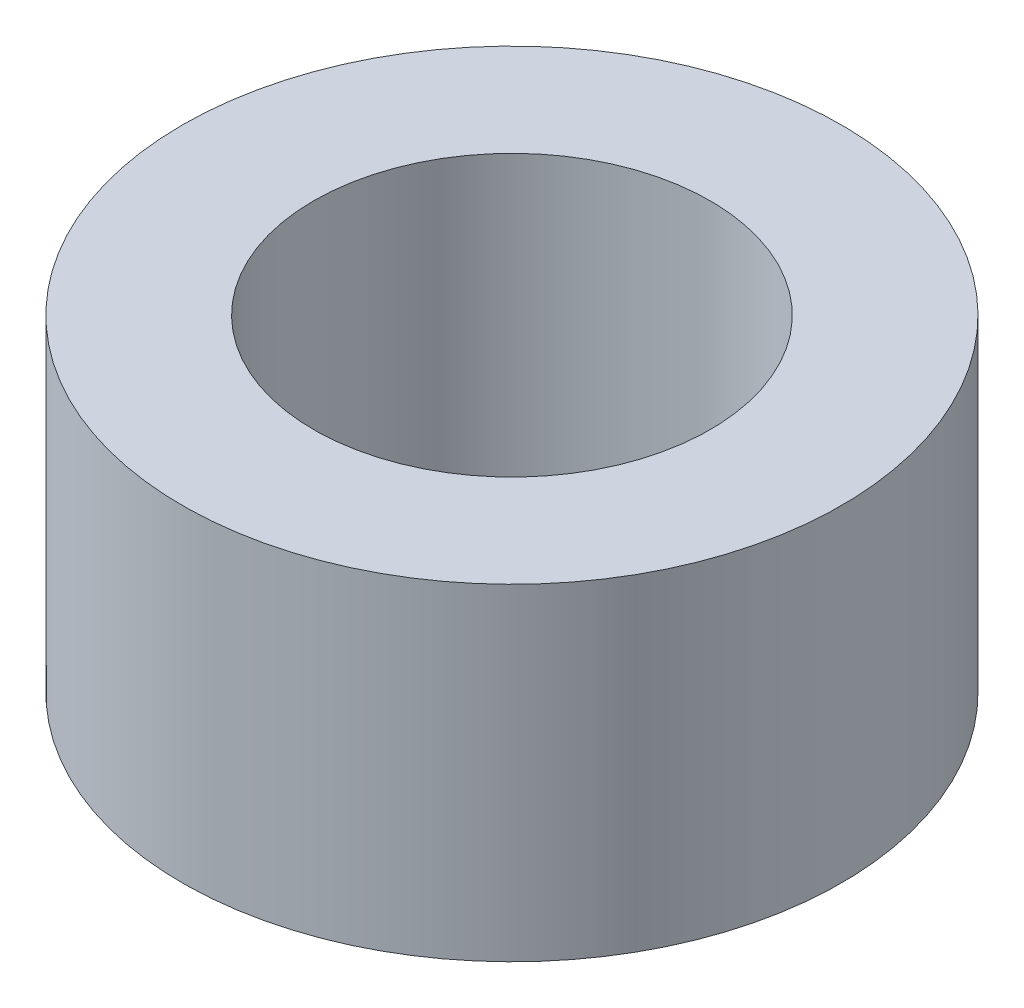
SolidWorks part; units mm, degrees
material "Alum Plate"
ref_plane "Front Plane" through (0, 0, 0) normal (0, 0, 1) x (1, 0, 0)
ref_plane "Top Plane" through (0, 0, 0) normal (0, 1, 0) x (1, 0, 0)
ref_plane "Right Plane" through (0, 0, 0) normal (1, 0, 0) x (0, 0, -1)
other "Bounding Box"
ref_plane "Default Plane" through (-8.9266, -12.7485, 0) normal (-0.1736, 0.9848, 0) x (0.9848, 0.1736, 0)
sketch "Sketch1" plane through (0, 0, 0) normal (0, 1, 0) x (1, 0, 0)
  line L0 (0, -12.5) -> (0, 12.5) construction
  line L1 (-14.5, 0) -> (0, 14.5) construction
  line L2 (-19.05, 19.05) -> (19.05, 19.05)
  line L3 (-19.05, 19.05) -> (-19.05, -19.05)
  line L4 (-19.05, -19.05) -> (19.05, -19.05)
  line L5 (19.05, 19.05) -> (19.05, -19.05)
  line L6 (-19.05, 19.05) -> (19.05, -19.05) construction
  line L7 (-19.05, -19.05) -> (19.05, 19.05) construction
  line L8 (8.8388, 8.8388) -> (-8.8388, 8.8388) construction
  line L9 (8.8388, 8.8388) -> (8.8388, -8.8388) construction
  line L10 (8.8388, -8.8388) -> (-8.8388, -8.8388) construction
  line L11 (-8.8388, 8.8388) -> (-8.8388, -8.8388) construction
  line L12 (8.8388, 8.8388) -> (-8.8388, -8.8388) construction
  line L13 (8.8388, -8.8388) -> (-8.8388, 8.8388) construction
  line L14 (-14.5, 0) -> (0, -14.5) construction
  line L15 (0, 14.5) -> (14.5, 0) construction
  line L16 (0, -14.5) -> (14.5, 0) construction
  line L17 (-14.5, 0) -> (14.5, 0) construction
  line L18 (0, 14.5) -> (0, -14.5) construction
  circle A0 centre (-15.24, 15.24) radius 1.3843 construction
  circle A1 centre (15.24, 15.24) radius 1.3843 construction
  circle A2 centre (15.24, -15.24) radius 1.3843 construction
  circle A3 centre (-15.24, -15.24) radius 1.3843 construction
  circle A4 centre (0, 0) radius 4
  circle A5 centre (8.8388, 8.8388) radius 1.5875
  circle A6 centre (8.8388, -8.8388) radius 1.5875
  circle A7 centre (-8.8388, -8.8388) radius 1.5875
  circle A8 centre (-8.8388, 8.8388) radius 1.5875
  circle A9 centre (-14.5, 0) radius 1.25
  circle A10 centre (0, 14.5) radius 1.25
  circle A11 centre (14.5, 0) radius 1.25
  circle A12 centre (0, -14.5) radius 1.25
  point P3 (0, 0)
  circle B0 centre (-9.8995, -9.8995) radius 1.2645 construction
  circle B1 centre (0, -8) radius 1.5875 construction
  circle B2 centre (0, 0) radius 4 construction
  circle B3 centre (9.8995, 9.8995) radius 1.2645 construction
  circle B4 centre (0, 8) radius 1.5875 construction
  circle B5 centre (9.8995, -9.8995) radius 1.2645 construction
  circle B6 centre (0, -12.5) radius 1.5875 construction
  circle B7 centre (-9.5, 0) radius 1.5875 construction
  circle B8 centre (-15.24, 15.24) radius 1.3843 construction
  circle B9 centre (15.24, 15.24) radius 1.3843 construction
  circle B10 centre (15.24, -15.24) radius 1.3843 construction
  circle B11 centre (-15.24, -15.24) radius 1.3843 construction
  circle B12 centre (9.5, 0) radius 1.5875 construction
  circle B13 centre (-9.8995, 9.8995) radius 1.2645 construction
  circle B14 centre (0, 12.5) radius 1.5875 construction
  dimension "D2" = 3.175
  dimension "D4" = 2.5
  dimension "D1" = 38.1
  dimension "D3" = 25
  dimension "D5" = 29
sketch_block_instance "Block-36mm gearbox motor block holes-1"
sketch_block "Block-36mm gearbox motor block holes"
extrude "Boss-Extrude1" add sketch "Sketch1" along normal mid plane 6.35
sketch "Sketch4" plane through (0, 0, 19.05) normal (0, 0, 1) x (1, 0, 0)
  line L0 (-5.5562, 0) -> (0, 0) construction
  line L1 (0, 0) -> (5.5562, 0) construction
  circle A0 centre (-5.5562, 0) radius 1.7272
  circle A1 centre (5.5562, 0) radius 1.7272
  dimension "D2" = 3.4544
  dimension "D1" = 11.1125
extrude "Cut-Extrude2" cut sketch "Sketch4" against normal blind 10.795
sketch "Sketch7" plane through (0, -3.175, 0) normal (0, -1, 0) x (1, 0, 0)
  line L0 (-19.05, 15.0813) -> (-15.0813, 15.0813) construction
  line L1 (-19.05, -19.05) -> (-19.05, 19.05) construction
  line L2 (-15.0813, 15.0813) -> (-15.0813, 19.05) construction
  line L3 (-19.05, 19.05) -> (19.05, 19.05) construction
  line L4 (0, 0) -> (-15.0813, 15.0813) construction
  line L5 (0, 0) -> (15.0813, 15.0812) construction
  circle A0 centre (-15.0813, 15.0813) radius 2.1526
  circle A1 centre (15.0813, 15.0812) radius 2.1527
  circle A2 centre (15.0812, -15.0813) radius 2.1527
  circle A3 centre (-15.0813, -15.0812) radius 2.1526
  dimension "D2" = 4.3053
  dimension "D1" = 3.9688
  dimension "D4" = 90
  dimension "D3" = 4
extrude "Cut-Extrude3" cut sketch "Sketch7" against normal through all
pattern_circular "CirPattern1" count 4 over 360 about axis through (0, 0, 0) along (0, 1, 0) of "Cut-Extrude2"
ref_plane "Plane1" through (0, -32.512, 0) normal (0, -1, 0) x (-1, 0, 0)
sketch "Sketch6" plane through (0, -32.512, 0) normal (0, -1, 0) x (-1, 0, 0)
  line L0 (19.05, 19.05) -> (-19.05, 19.05) construction
  line L1 (19.05, 19.05) -> (19.05, -19.05) construction
  line L2 (19.05, -19.05) -> (-19.05, -19.05) construction
  line L3 (-19.05, 19.05) -> (-19.05, -19.05) construction
  line L12 (19.05, 19.05) -> (-19.05, 19.05)
  line L13 (19.05, 19.05) -> (19.05, -19.05)
  line L14 (19.05, -19.05) -> (-19.05, -19.05)
  line L15 (-19.05, 19.05) -> (-19.05, -19.05)
  circle A8 centre (0, 0) radius 6.5
  circle A17 centre (-15.0812, 15.0813) radius 2.1526
  circle A18 centre (15.0813, 15.0812) radius 2.1526
  circle A19 centre (15.0813, -15.0813) radius 2.1527
  circle A20 centre (-15.0813, -15.0812) radius 2.1526
  circle A21 centre (-15.0812, 15.0813) radius 2.1527 construction
  dimension "D2" = 13
extrude "Boss-Extrude2" add sketch "Sketch6" along normal blind 3.175 separate body
fillet "Fillet1" radius 2.54 4 edges at (-19.05, 0, 19.05) (-19.05, 0, -19.05) (19.05, 0, -19.05) (19.05, 0, 19.05)
fillet "Fillet2" radius 2.54 4 edges at (-19.05, -34.0995, 19.05) (-19.05, -34.0995, -19.05) (19.05, -34.0995, -19.05) (19.05, -34.0995, 19.05)
sketch "Sketch8" plane through (0, -32.512, 0) normal (0, 1, 0) x (1, 0, 0)
  line L0 (-16.51, 19.05) -> (16.51, 19.05) construction
  circle A0 centre (-15.0813, 15.0812) radius 2.3876
  circle A1 centre (-15.0813, 15.0812) radius 3.9688
  dimension "D1" = 4.7752
extrude "Boss-Extrude3" add sketch "Sketch8" along normal offset from surface (3.937 mm away) 25.4 separate body up to face at (-15.0813, -3.175, -17.2339)
pattern_circular "CirPattern2" count 4 over 360 about axis through (0, 0, 0) along (0, 1, 0) of bodies 110
delete or keep bodies "Body-Delete/Keep 1" [suppressed] type keep bodies bodies 108
delete or keep bodies "Body-Delete/Keep 2" [suppressed] type keep bodies bodies 107
delete or keep bodies "Body-Delete/Keep 3" bodies 113
